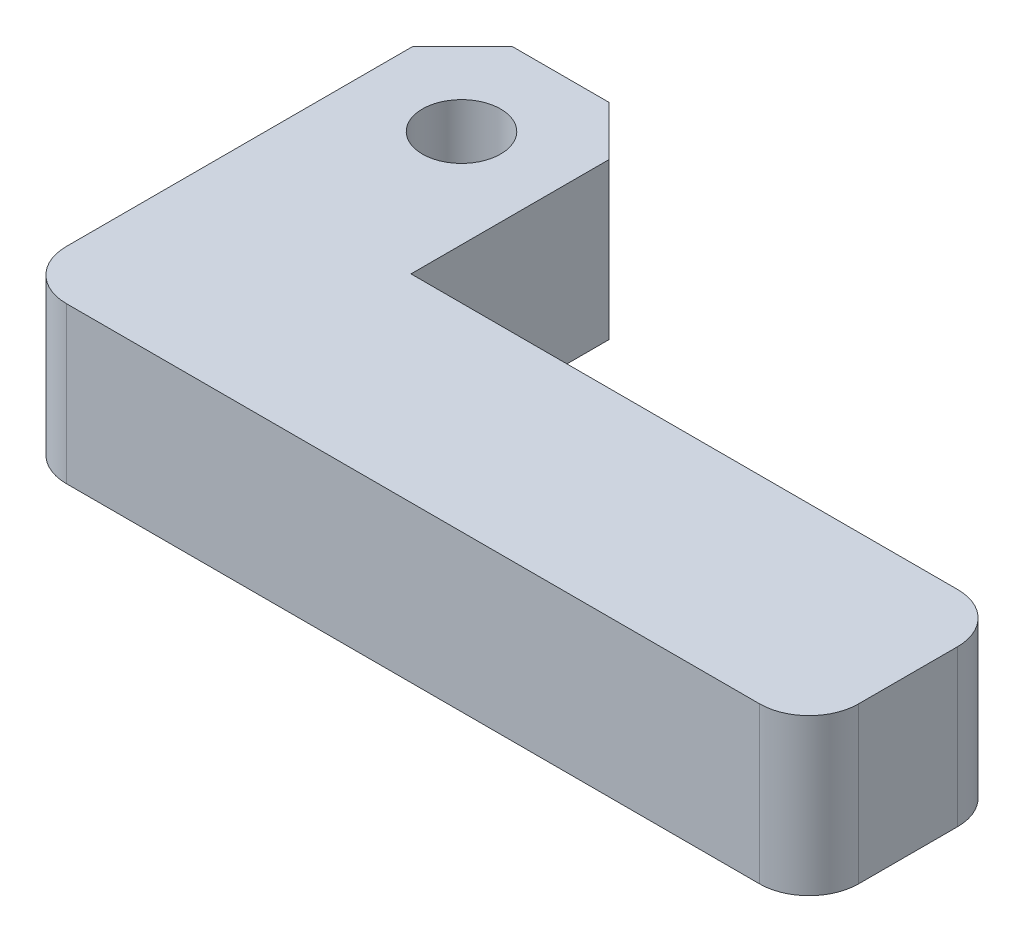
SolidWorks part; units mm, degrees
ref_plane "Front" through (0, 0, 0) normal (0, 0, 1) x (1, 0, 0)
ref_plane "Top" through (0, 0, 0) normal (0, 1, 0) x (1, 0, 0)
ref_plane "Right" through (0, 0, 0) normal (1, 0, 0) x (0, 0, -1)
sketch "Sketch1" plane through (0, 0, 0) normal (0, 1, 0) x (1, 0, 0)
  line L0 (0, 28.575) -> (0, 0)
  line L1 (0, 0) -> (47.625, 0)
  line L2 (50.8, 3.175) -> (50.8, 9.525)
  line L3 (47.625, 12.7) -> (12.573, 12.7)
  line L4 (12.573, 12.7) -> (12.573, 28.575)
  line L5 (12.573, 28.575) -> (0, 28.575)
  circle A0 centre (6.2865, 22.225) radius 2.5083
  arc A1 (47.625, 0) -> (50.8, 3.175) centre (47.625, 3.175) ccw
  arc A2 (50.8, 9.525) -> (47.625, 12.7) centre (47.625, 9.525) ccw
  point P6 (0, 0)
  point P10 (6.2865, 28.575)
  point P11 (0, 0)
  point P14 (50.8, 0)
  dimension "D4" = 5.0165
  dimension "D6" = 3.175
  dimension "D1" = 12.573
  dimension "D2" = 28.575
  dimension "D3" = 50.8
  dimension "D5" = 6.35
  dimension "D7" = 12.7
extrude "Boss-Extrude1" add sketch "Sketch1" along normal blind 10
fillet "Fillet1" radius 3.175 1 edges at (0, 5, 0)
chamfer "Chamfer1" distance 3.175 angle 45 2 edges at (0, 5, -28.575) (12.573, 5, -28.575)
